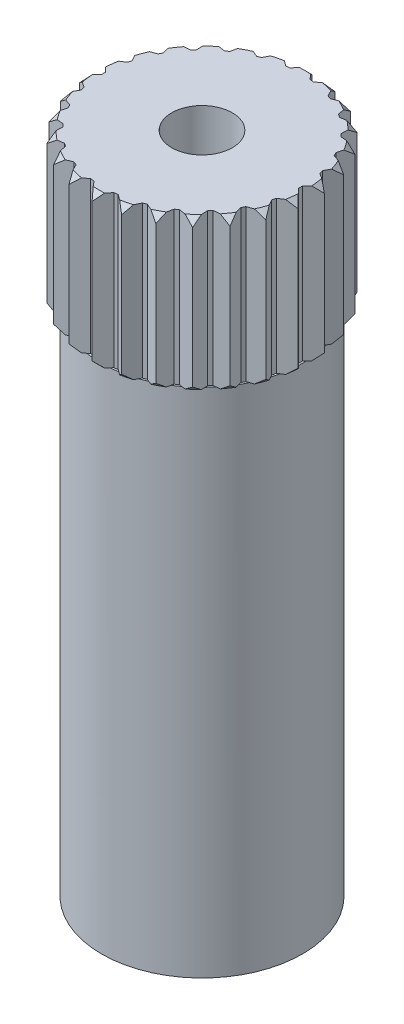
SolidWorks part; units mm, degrees
material "Brass"
ref_plane "Front Plane" through (0, 0, 0) normal (0, 0, 1) x (1, 0, 0)
ref_plane "Top Plane" through (0, 0, 0) normal (0, 1, 0) x (1, 0, 0)
ref_plane "Right Plane" through (0, 0, 0) normal (1, 0, 0) x (0, 0, -1)
sketch "ShaftS" plane through (0, 0, 0) normal (0, 1, 0) x (1, 0, 0)
  circle A0 centre (0, 0) radius 2.9
  dimension "D1" = 5.8
extrude "SHAFT" add sketch "ShaftS" along normal blind 13.5
sketch "ShaftExtensionS" plane through (0, 13.5, 0) normal (0, 1, 0) x (1, 0, 0)
  circle A0 centre (0, 0) radius 2.6
  circle A1 centre (0, 0) radius 2.9 construction
  dimension "D1" = 0.3
extrude "SHAFT EXTENSION" add sketch "ShaftExtensionS" along normal blind 4
sketch "ToothS" plane through (0, 17.5, 0) normal (0, 1, 0) x (1, 0, 0)
  line L0 (0, 2.6) -> (0, 2.9) construction
  line L1 (0, 2.9) -> (-0.2629, 2.5867)
  line L2 (0, 2.9) -> (0.2629, 2.5867)
  line L3 (-0.2629, 2.5867) -> (0.2629, 2.5867) construction
  arc A0 (0.2629, 2.5867) -> (-0.2629, 2.5867) centre (0, 0) ccw
  circle A3 centre (0, 0) radius 2.6 construction
  circle A4 centre (0, 0) radius 2.9 construction
  dimension "D1" = 80
  dimension "D2" = 0.5258
  dimension "D3" = 0.3
extrude "TOOTH" add sketch "ToothS" against normal up to body (17.5 mm away) separate body
pattern_circular "TOOTH CP" count 26 over 360 about axis through (0, 0, 0) along (0, 1, 0) of "TOOTH"
sketch "SmallBoreS" plane through (0, 17.5, 0) normal (0, 1, 0) x (1, 0, 0)
  circle A0 centre (0, 0) radius 0.8
  dimension "D1" = 1.6
extrude "SMALL BORE" cut sketch "SmallBoreS" against normal blind 4
sketch "ShaftUnderCutS" plane through (0, 0, 0) normal (0, 0, 1) x (1, 0, 0)
  line L0 (2.9, 0) -> (2.65, 0)
  line L1 (2.65, 0) -> (2.65, 13.5)
  line L2 (2.65, 13.5) -> (2.9, 13.5)
  line L3 (2.9, 13.5) -> (2.9, 0)
  line L4 (0, 0) -> (2.65, 0) construction
  line L5 (2.7115, 13.5) -> (2.3867, 13.5) construction
  line L6 (0, 13.5) -> (0, 0) construction
  dimension "D1" = 0.25
  dimension "D2" = 2.65
  dimension "D3" = 2.9
revolve "SHAFT UNDER CUT" cut sketch "ShaftUnderCutS" angle 360 about axis through (0, 13.5, 0) along (0, -1, 0)
sketch "TeethChamferS" plane through (0, 0, 0) normal (1, 0, 0) x (0, 0, -1)
  line L0 (2.9, 17.3232) -> (2.9, 17.5)
  line L1 (2.9, 17.5) -> (2.7232, 17.5)
  line L2 (2.7232, 17.5) -> (2.9, 17.3232)
  line L3 (2.9, 13.5) -> (2.9, 17.5) construction
  line L4 (2.9, 15.5) -> (0, 15.5) construction
  line L5 (0, 17.5) -> (0, 13.5) construction
  line L6 (2.7232, 13.5) -> (2.9, 13.6768)
  line L7 (2.9, 13.5) -> (2.7232, 13.5)
  line L8 (2.9, 13.6768) -> (2.9, 13.5)
  point P4 (2.9, 15.5)
  dimension "D1" = 45
  dimension "D2" = 0.25
revolve "TEETH CHAMFER" cut sketch "TeethChamferS" angle 360 about axis through (0, 13.5, 0) along (0, 1, 0)
